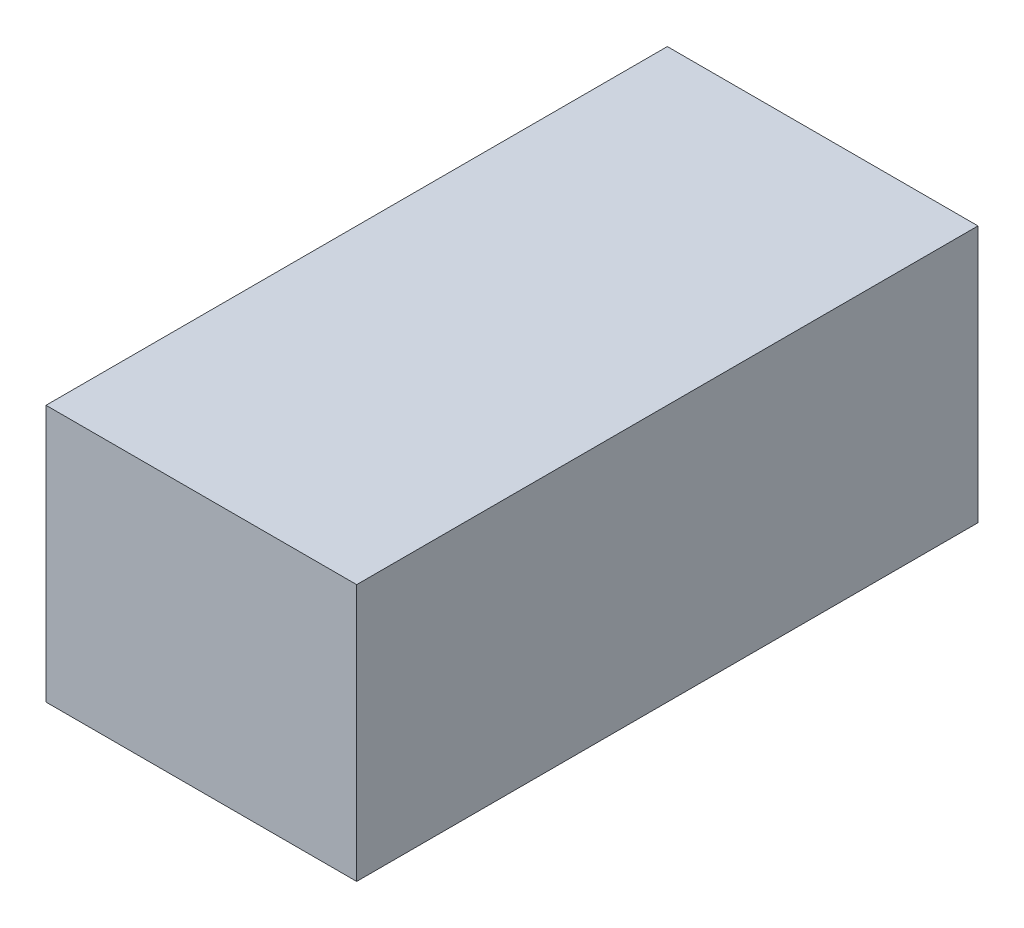
SolidWorks part; units mm, degrees
ref_plane "Plan de face" through (0, 0, 0) normal (0, 0, 1) x (1, 0, 0)
ref_plane "Plan de dessus" through (0, 0, 0) normal (0, 1, 0) x (1, 0, 0)
ref_plane "Plan de droite" through (0, 0, 0) normal (1, 0, 0) x (0, 0, -1)
sketch "Esquisse1" plane through (0, 0, 0) normal (0, 0, 1) x (1, 0, 0)
  line L4 (-0.3, 2.8) -> (-0.3, 2.3863)
  line L6 (-0.8, 2.8) -> (-0.8, 2.3863)
  line L8 (-0.8, 2.8) -> (-0.3, 2.8)
  line L9 (-0.8, 2.3863) -> (-0.3, 2.3863)
extrude "Boss.-Extru.1" add sketch "Esquisse1" along normal blind 1
